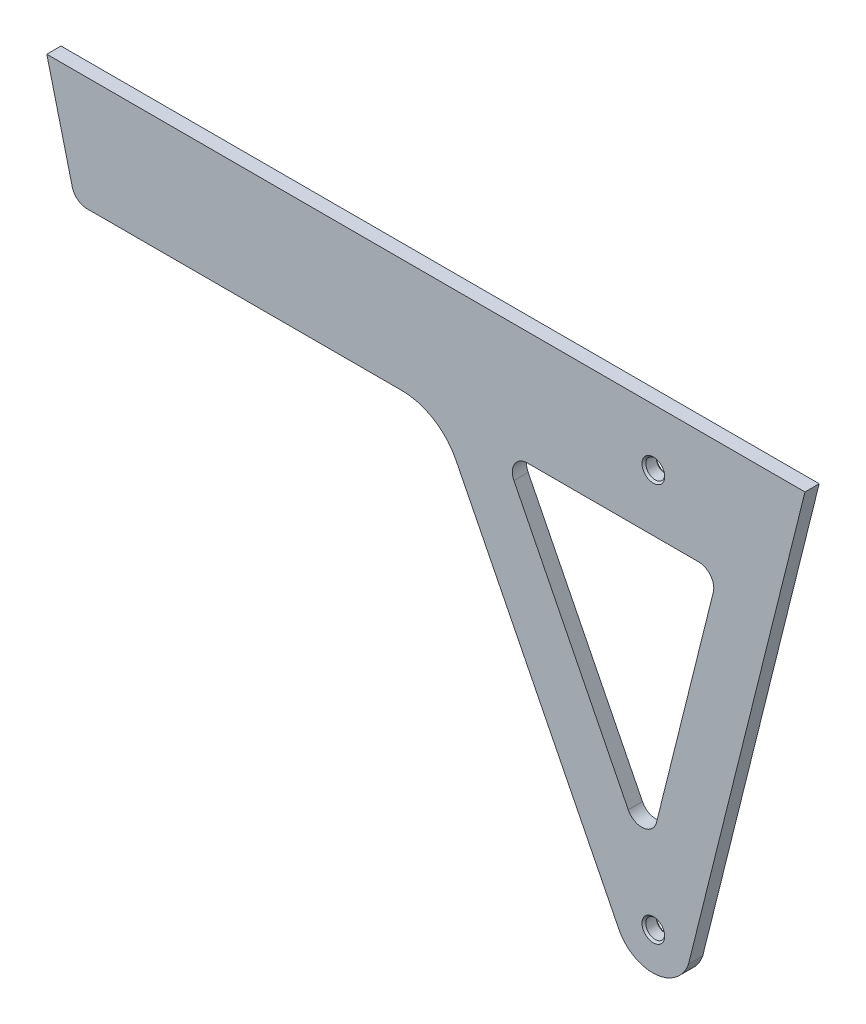
SolidWorks part; units mm, degrees
material "6061-T6 (SS)"
ref_plane "Front Plane" through (0, 0, 0) normal (0, 0, 1) x (1, 0, 0)
ref_plane "Top Plane" through (0, 0, 0) normal (0, 1, 0) x (1, 0, 0)
ref_plane "Right Plane" through (0, 0, 0) normal (1, 0, 0) x (0, 0, -1)
sketch "Sketch1" plane through (0, 0, 0) normal (0, 0, 1) x (1, 0, 0)
  line L0 (0, 0) -> (254, 0)
  line L9 (254, 0) -> (214.9703, -156.5394)
  line L10 (137.1206, -49.3112) -> (191.6359, -158.0223)
  line L11 (0, 0) -> (8.5392, -34.249)
  line L12 (13.4683, -38.1) -> (118.9847, -38.1)
  arc A1 (191.6359, -158.0223) -> (214.9703, -156.5394) centre (202.9885, -152.3293) ccw
  arc A2 (137.1206, -49.3112) -> (118.9847, -38.1) centre (118.9565, -58.42) ccw
  arc A3 (8.5392, -34.249) -> (13.4683, -38.1) centre (13.4683, -33.02) ccw
  point P19 (9.4994, -38.1)
  dimension "D9" = 214.9703
  dimension "D6" = 20.32
  dimension "D4" = 12.7
  dimension "D12" = 5.08
  dimension "D2" = 34.249
  dimension "D5" = 254
  dimension "D10" = 38.1
  dimension "D11" = 38.1
  dimension "D15" = 152.3293
  dimension "D16" = 202.9885
  dimension "D17" = 118.9847
  dimension "D18" = 137.1206
extrude "Boss-Extrude1" add sketch "Sketch1" along normal blind 4.7625 contours L10 A1 L9 L0 L11 A3 L12 A2
sketch "Sketch3" plane through (0, 0, 4.7625) normal (0, 0, 1) x (1, 0, 0)
  line L0 (203.2, -165.0276) -> (203.2, 0) construction
  line L1 (0, 0) -> (254, 0) construction
  arc A1 (191.6359, -158.0223) -> (214.9703, -156.5394) centre (202.9885, -152.3293) ccw construction
  circle A2 centre (203.2, -152.4) radius 3.175
  circle A3 centre (203.2, -19.05) radius 3.175
  dimension "D2" = 152.4
  dimension "D3" = 19.05
  dimension "D4" = 6.35
  dimension "D5" = 6.35
  dimension "D1" = 50.8
extrude "Cut-Extrude1" cut sketch "Sketch3" against normal blind 4.7625
sketch "Sketch4" plane through (0, 0, 4.7625) normal (0, 0, 1) x (1, 0, 0)
  line L0 (161.04, -38.1) -> (218.3653, -38.1) construction
  line L1 (254, 0) -> (214.9703, -156.5394) construction
  line L8 (161.04, -38.1) -> (218.3653, -38.1)
  line L11 (223.2944, -44.409) -> (204.2576, -120.7615)
  line L12 (194.7875, -121.8097) -> (156.499, -45.4572)
  arc A0 (204.2576, -120.7615) -> (194.7875, -121.8097) centre (199.3285, -119.5325) cw
  arc A1 (161.04, -38.1) -> (156.499, -45.4572) centre (161.04, -43.18) ccw
  arc A2 (223.2944, -44.409) -> (218.3653, -38.1) centre (218.3653, -43.18) ccw
  point P19 (152.8096, -38.1)
  dimension "D2" = 5.08
  dimension "D4" = 5.08
  dimension "D5" = 5.08
  dimension "D3" = 19.05
extrude "Cut-Extrude2" cut sketch "Sketch4" against normal blind 4.7625 contours L12 A1 L8 A2 L11 A0
chamfer "Chamfer2" distance 0.635 1 edges at (206.375, -152.4, 4.7625)
chamfer "Chamfer3" distance 0.635 1 edges at (206.375, -19.05, 4.7625)
chamfer "Chamfer4" distance 0.635 1 edges at (206.375, -19.05, 0)
chamfer "Chamfer5" distance 0.635 1 edges at (206.375, -152.4, 0)
